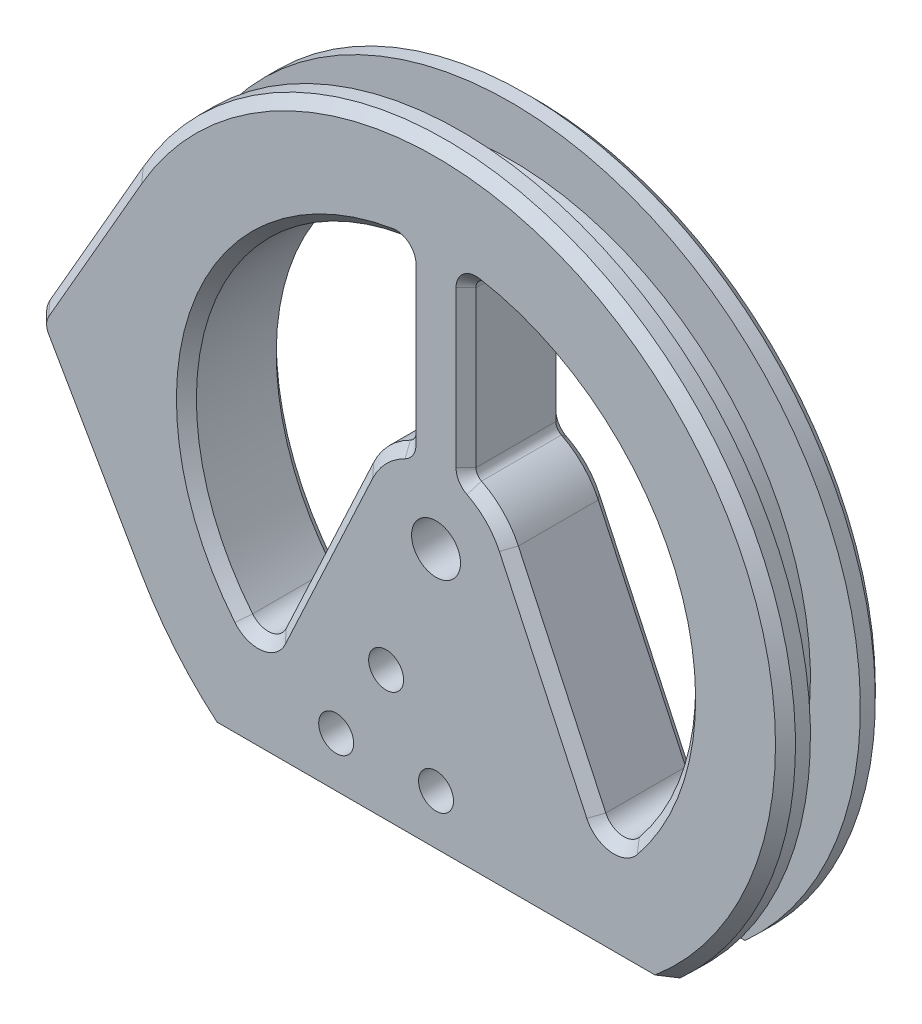
SolidWorks part; units mm, degrees
ref_plane "正面(Front)" through (0, 0, 0) normal (0, 0, 1) x (1, 0, 0)
ref_plane "平面(Top)" through (0, 0, 0) normal (0, 1, 0) x (1, 0, 0)
ref_plane "右側面(Right)" through (0, 0, 0) normal (1, 0, 0) x (0, 0, -1)
sketch "ｽｹｯﾁ1" plane through (0, 0, 0) normal (0, 0, 1) x (1, 0, 0)
  line L0 (-15, -25.9808) -> (15, -25.9808)
  line L1 (-13.5944, -20.9808) -> (13.5944, -20.9808)
  arc A0 (-15, -25.9808) -> (15, -25.9808) centre (0, 0) cw
  arc A2 (-13.5944, -20.9808) -> (13.5944, -20.9808) centre (0, 0) cw
  dimension "D1" = 30
  dimension "D2" = 30
  dimension "D3" = 5
extrude "ﾎﾞｽ - 押し出し1" add sketch "ｽｹｯﾁ1" along normal blind 10
sketch "ｽｹｯﾁ2" plane through (0, 0, 0) normal (0, 0, 1) x (1, 0, 0)
  line L2 (-13.5944, -20.9808) -> (13.5944, -20.9808)
  line L3 (-7.2505, 3.3809) -> (-17.2604, -18.0854)
  line L4 (7.2505, 3.3809) -> (17.2604, -18.0854)
  line L5 (0, 0) -> (0, -43.0761) construction
  arc A0 (7.2505, 3.3809) -> (-7.2505, 3.3809) centre (0, 0) ccw
  circle A1 centre (0, 0) radius 2.45
  arc A2 (13.5944, -20.9808) -> (-13.5944, -20.9808) centre (0, 0) ccw construction
  arc A3 (13.5944, -20.9808) -> (17.2604, -18.0854) centre (0, 0) ccw
  arc A4 (-17.2604, -18.0854) -> (-13.5944, -20.9808) centre (0, 0) ccw
  dimension "D1" = 8
  dimension "D2" = 4.9
  dimension "D3" = 25
extrude "ﾎﾞｽ - 押し出し2" add sketch "ｽｹｯﾁ2" along normal blind 10
sketch "ｽｹｯﾁ3" plane through (0, 0, 10) normal (0, 0, 1) x (1, 0, 0)
  line L0 (-15, -25.9808) -> (15, -25.9808) construction
  circle A0 centre (0, -20.9808) radius 1.75
  circle A1 centre (-10, -20.9808) radius 1.75
  dimension "D1" = 3.5
  dimension "D2" = 5
  dimension "D3" = 10
extrude "ｶｯﾄ - 押し出し1" cut sketch "ｽｹｯﾁ3" against normal through all
sketch "ｽｹｯﾁ4" plane through (0, 0, 0) normal (0, 0, 1) x (1, 0, 0)
  line L0 (-15, -25.9808) -> (15, -25.9808) construction
  line L1 (-23.4521, -25.9808) -> (-15, -25.9808)
  line L2 (15, -25.9808) -> (23.4521, -25.9808)
  arc A1 (15, -25.9808) -> (-15, -25.9808) centre (0, 0) ccw construction
  arc A2 (17.5, -30.3109) -> (-17.5, -30.3109) centre (0, 0) ccw
  arc A3 (23.4521, -25.9808) -> (-23.4521, -25.9808) centre (0, 0) ccw
  arc A4 (15, -25.9808) -> (-15, -25.9808) centre (0, 0) ccw
  dimension "D1" = 5
extrude "ﾎﾞｽ - 押し出し3" add sketch "ｽｹｯﾁ4" along normal blind 2.5
ref_plane "平面1" through (0, 0, 5) normal (0, 0, -1) x (-1, 0, 0)
sketch "ｽｹｯﾁ5" plane through (0, 0, 0) normal (0, 0, 1) x (1, 0, 0)
  line L0 (0, 0) -> (-37.5, 0) construction
  line L1 (-30.3333, 17.4611) -> (-39.6667, 1.2472)
  line L6 (-39.6667, -1.2472) -> (-30.3333, -17.4611)
  line L7 (-30.3333, 17.4611) -> (-30.3333, -17.4611)
  arc A3 (-39.6667, 1.2472) -> (-39.6667, -1.2472) centre (-37.5, 0) ccw
  arc A4 (23.4521, -25.9808) -> (-23.4521, -25.9808) centre (0, 0) ccw construction
  dimension "D1" = 2.5
  dimension "D2" = 2.5
extrude "ﾎﾞｽ - 押し出し4" add sketch "ｽｹｯﾁ5" along normal blind 2.5
mirror "ﾐﾗｰ2" about plane through (0, 0, 5) normal (0, 0, -1) of "ﾎﾞｽ - 押し出し3", "ﾎﾞｽ - 押し出し4"
sketch "ｽｹｯﾁ6" plane through (0, 0, 2.5) normal (0, 0, 1) x (1, 0, 0)
  circle A0 centre (-37.5, 0) radius 2.5
  arc A1 (-39.6667, 1.2472) -> (-39.6667, -1.2472) centre (-37.5, 0) ccw construction
extrude "ﾎﾞｽ - 押し出し5" add sketch "ｽｹｯﾁ6" along normal up to next
fillet "ﾌｨﾚｯﾄ1" radius 2 2 edges at (17.2604, -18.0854, 5) (-17.2604, -18.0854, 5)
sketch "ｽｹｯﾁ7" plane through (0, 0, 10) normal (0, 0, 1) x (1, 0, 0)
  line L1 (-3, 27) -> (3, 27)
  line L2 (-3, 27) -> (-3, 5)
  line L3 (-3, 5) -> (3, 5)
  line L4 (3, 27) -> (3, 5)
  line L5 (-3, 27) -> (3, 5) construction
  line L6 (-3, 5) -> (3, 27) construction
  point P0 (0, 16)
  dimension "D1" = 6
  dimension "D2" = 5
  dimension "D3" = 22
extrude "ﾎﾞｽ - 押し出し6" add sketch "ｽｹｯﾁ7" against normal up to surface (10 mm away) up to face at (-19.206, -3.4574, 0)
fillet "ﾌｨﾚｯﾄ2" radius 1 4 edges at (-3, 24.8193, 5) (3, 24.8193, 5) (3, 7.4162, 5) (-3, 7.4162, 5)
chamfer "面取り1" distance 1 angle 45 28 edges at (-3, 15.8633, 10) (-3, 15.8633, 0) (-3.3545, 24.4281, 0) (-3.1502, 7.5352, 0) (-23.4032, 8.7914, 0) (-5.7249, 5.5879, 10) (-5.7249, 5.5879, 0) (-17.5688, -16.5302, 0) (-11.6272, -6.0049, 0) (-11.6272, -6.0049, 10) (-3.3545, 24.4281, 10) (-3.1502, 7.5352, 10) (-23.4032, 8.7914, 10) (-17.5688, -16.5302, 10) (5.7249, 5.5879, 0) (5.7249, 5.5879, 10) (3.1502, 7.5352, 0) (11.6272, -6.0049, 10) (11.6272, -6.0049, 0) (3, 15.8633, 0) (3, 15.8633, 10) (17.5688, -16.5302, 0) (3.3545, 24.4281, 0) (23.4032, 8.7914, 0) (3.1502, 7.5352, 10) (17.5688, -16.5302, 10) (3.3545, 24.4281, 10) (23.4032, 8.7914, 10)
chamfer "面取り2" distance 1 angle 45 10 edges at (21.9917, 27.228, 0) (-27.228, -21.9917, 0) (-35, 9.3541, 0) (-40, 0, 0) (-35, -9.3541, 0) (21.9917, 27.228, 10) (-27.228, -21.9917, 10) (-35, 9.3541, 10) (-40, 0, 10) (-35, -9.3541, 10)
sketch "ｽｹｯﾁ8" plane through (0, 0, 10) normal (0, 0, 1) x (1, 0, 0)
  circle A0 centre (-5, -12.9808) radius 1.75
  circle A1 centre (0, -20.9808) radius 1.75 construction
  dimension "D1" = 3.5
  dimension "D2" = 8
  dimension "D3" = 5
extrude "ｶｯﾄ - 押し出し2" cut sketch "ｽｹｯﾁ8" against normal through all
